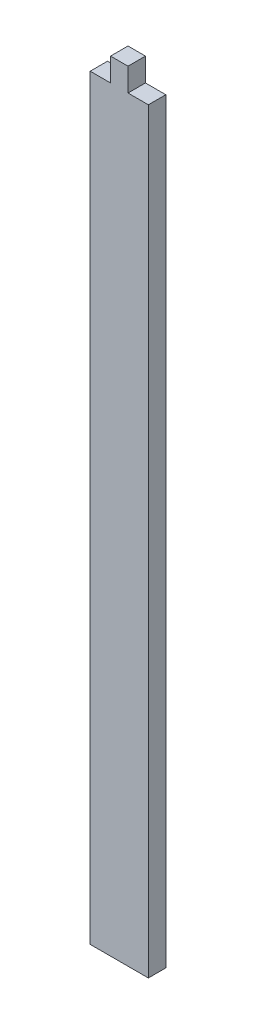
SolidWorks part; units mm, degrees
ref_plane "Front Plane" through (0, 0, 0) normal (0, 0, 1) x (1, 0, 0)
ref_plane "Top Plane" through (0, 0, 0) normal (0, 1, 0) x (1, 0, 0)
ref_plane "Right Plane" through (0, 0, 0) normal (1, 0, 0) x (0, 0, -1)
sketch "Sketch1" plane through (0, 0, 0) normal (0, 0, 1) x (1, 0, 0)
  line L0 (1.5, 65) -> (5, 65)
  line L1 (-5, 65) -> (-1.5, 65)
  line L2 (-5, 65) -> (-5, -65)
  line L3 (-5, -65) -> (5, -65)
  line L4 (5, 65) -> (5, -65)
  line L5 (-5, 65) -> (5, -65) construction
  line L6 (-5, -65) -> (5, 65) construction
  line L8 (-1.5, 65) -> (-1.5, 69)
  line L9 (-1.5, 69) -> (1.5, 69)
  line L10 (1.5, 65) -> (1.5, 69)
  point P0 (0, 0)
  dimension "D1" = 130
  dimension "D2" = 10
  dimension "D3" = 3
  dimension "D4" = 4
  dimension "D5" = 3.5
extrude "Boss-Extrude1" add sketch "Sketch1" along normal mid plane 3
